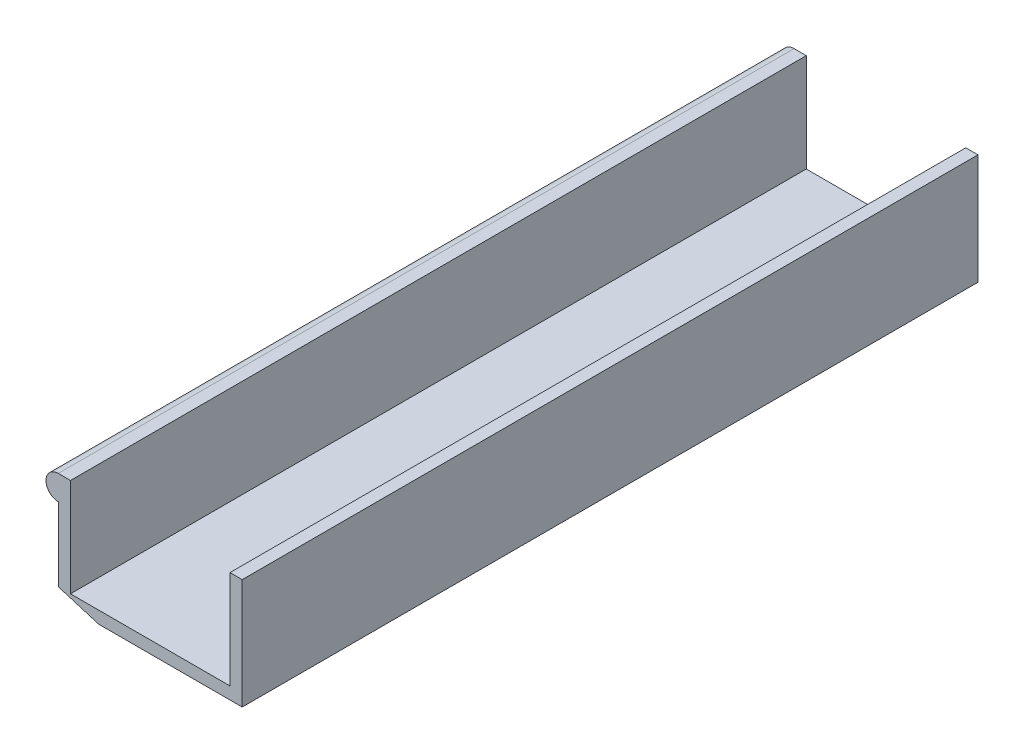
SolidWorks part; units mm, degrees
ref_plane "前基準面" through (0, 0, 0) normal (0, 0, 1) x (1, 0, 0)
ref_plane "上基準面" through (0, 0, 0) normal (0, 1, 0) x (1, 0, 0)
ref_plane "右基準面" through (0, 0, 0) normal (1, 0, 0) x (0, 0, -1)
sketch "草圖1" plane through (0, 0, 0) normal (0, 0, 1) x (1, 0, 0)
  line L0 (-111.2456, 70) -> (-111.2456, 10)
  line L1 (-111.2456, 10) -> (-78.2717, 0)
  line L2 (-78.2717, 0) -> (38.7544, 0)
  line L3 (38.7544, 0) -> (38.7544, 90)
  line L4 (5.0463, 9.9508) -> (5.0463, 0) construction
  line L5 (-101.2948, 90) -> (-101.2948, 9.9508)
  line L6 (28.8036, 90) -> (28.8036, 9.9508)
  line L7 (-101.2948, 9.9508) -> (28.8036, 9.9508)
  line L8 (-111.2456, 90) -> (-101.2948, 90)
  line L9 (28.8036, 90) -> (38.7544, 90)
  arc A0 (-111.2456, 90) -> (-111.2456, 70) centre (-111.2456, 80) ccw
  dimension "D2" = 10
  dimension "D1" = 90
  dimension "D3" = 60
  dimension "D4" = 150
extrude "填料-伸長1" add sketch "草圖1" along normal blind 600
